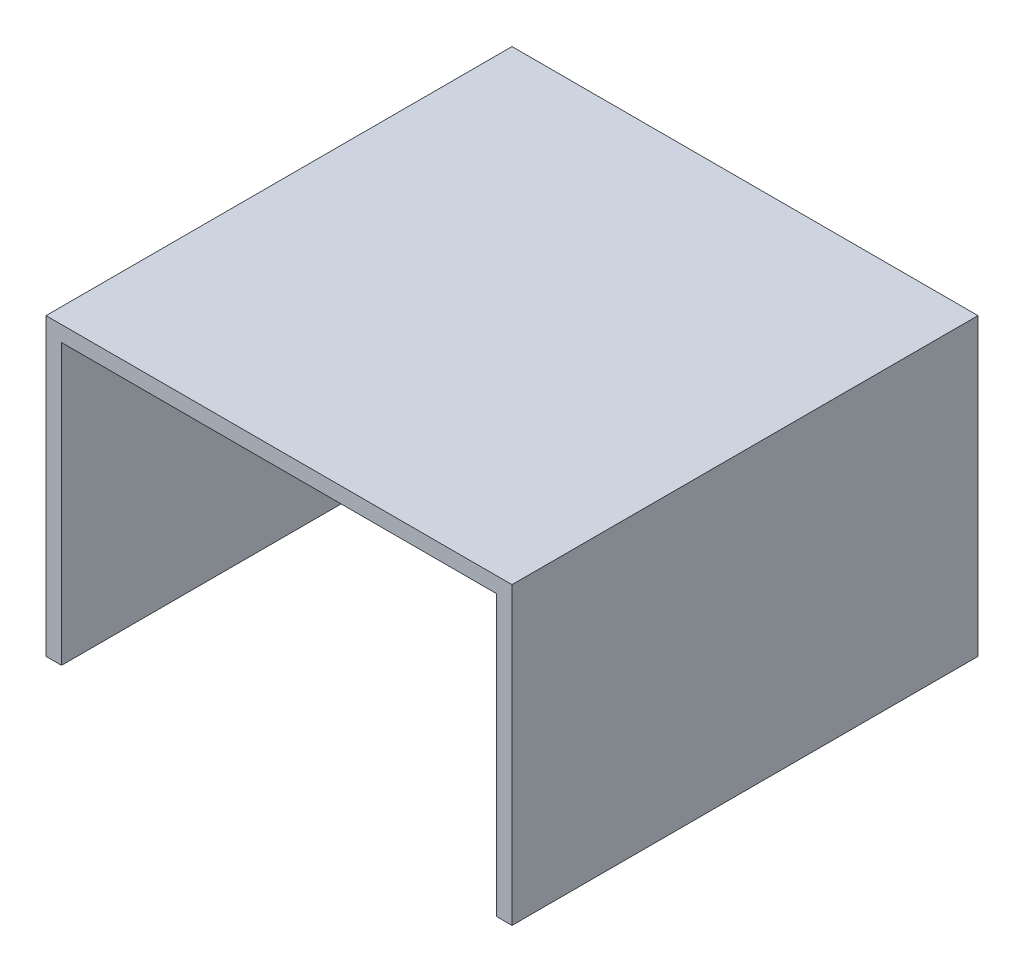
SolidWorks part; units mm, degrees
ref_plane "Front" through (0, 0, 0) normal (0, 0, 1) x (1, 0, 0)
ref_plane "Top" through (0, 0, 0) normal (0, 1, 0) x (1, 0, 0)
ref_plane "Right" through (0, 0, 0) normal (1, 0, 0) x (0, 0, -1)
sketch "Sketch1" plane through (0, 0, 0) normal (0, 1, 0) x (1, 0, 0)
  line L1 (-25.0287, 13.6697) -> (34.9713, 13.6697)
  line L2 (-25.0287, 13.6697) -> (-25.0287, -46.3303)
  line L3 (-25.0287, -46.3303) -> (34.9713, -46.3303)
  line L4 (34.9713, 13.6697) -> (34.9713, -46.3303)
  dimension "D1" = 60
  dimension "D2" = 60
extrude "Boss-Extrude1" add sketch "Sketch1" along normal blind 2
sketch "Sketch2" plane through (0, 0, 0) normal (0, -1, 0) x (1, 0, 0)
  line L0 (34.9713, -13.6697) -> (-25.0287, -13.6697) construction
  line L1 (34.9713, 46.3303) -> (32.9713, 46.3303)
  line L2 (34.9713, 46.3303) -> (34.9713, -13.6697)
  line L3 (34.9713, -13.6697) -> (32.9713, -13.6697)
  line L4 (32.9713, 46.3303) -> (32.9713, -13.6697)
  line L6 (-25.0287, 46.3303) -> (-23.0287, 46.3303)
  line L7 (-25.0287, 46.3303) -> (-25.0287, -13.6697)
  line L8 (-25.0287, -13.6697) -> (-23.0287, -13.6697)
  line L9 (-23.0287, 46.3303) -> (-23.0287, -13.6697)
  dimension "D1" = 2
  dimension "D2" = 2
extrude "Boss-Extrude2" add sketch "Sketch2" along normal blind 36
